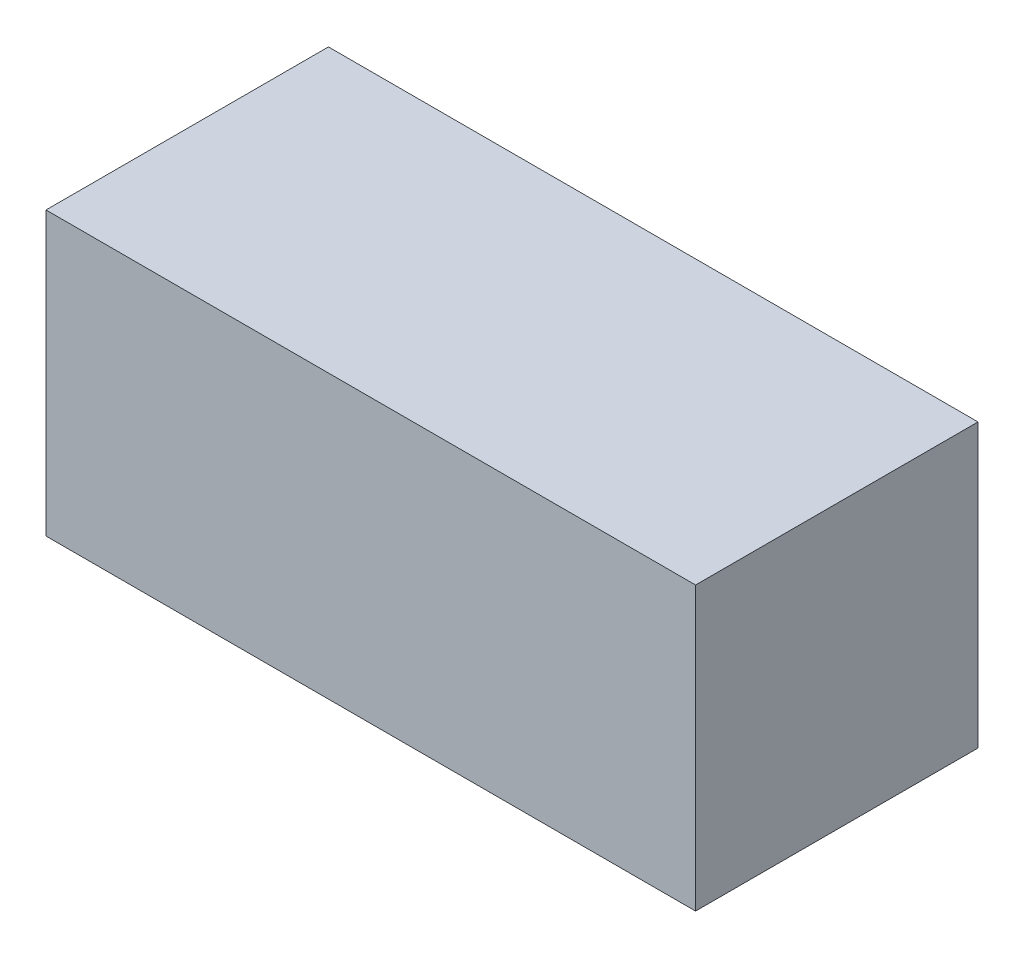
SolidWorks part; units mm, degrees
ref_plane "Front Plane" through (0, 0, 0) normal (0, 0, 1) x (1, 0, 0)
ref_plane "Top Plane" through (0, 0, 0) normal (0, 1, 0) x (1, 0, 0)
ref_plane "Right Plane" through (0, 0, 0) normal (1, 0, 0) x (0, 0, -1)
sketch "Sketch1" plane through (0, 0, 0) normal (0, 0, 1) x (1, 0, 0)
  line L0 (-6.75, 15.8) -> (6.75, 15.8) construction
  line L1 (-5.75, 26.3) -> (5.75, 26.3)
  line L2 (-5.75, 26.3) -> (-5.75, 21.3)
  line L3 (-5.75, 21.3) -> (5.75, 21.3)
  line L4 (5.75, 26.3) -> (5.75, 21.3)
  line L5 (-5.75, 26.3) -> (5.75, 21.3) construction
  line L6 (-5.75, 21.3) -> (5.75, 26.3) construction
  line L7 (-6.75, 31.8) -> (-6.75, 15.8) construction
  point P0 (0, 23.8)
  point P8 (0, 15.8)
  point P11 (-6.75, 23.8)
  dimension "D1" = 11.5
  dimension "D2" = 5
extrude "Boss-Extrude1" add sketch "Sketch1" along normal blind 5
